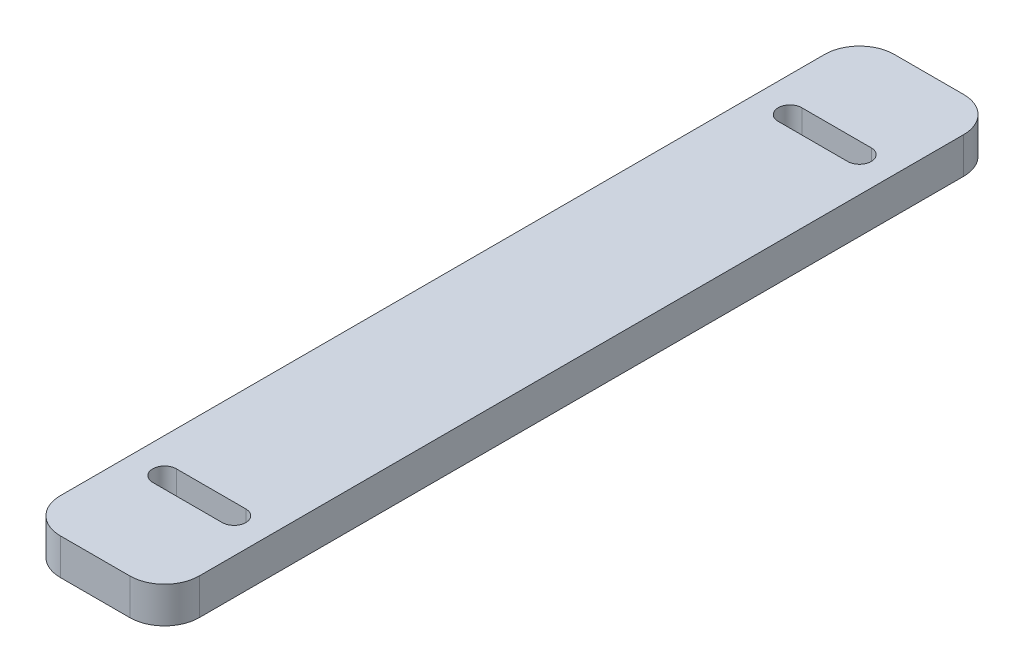
SolidWorks part; units mm, degrees
material "Acrylic (BLUE)"
ref_plane "Front Plane" through (0, 0, 0) normal (0, 0, 1) x (1, 0, 0)
ref_plane "Top Plane" through (0, 0, 0) normal (0, 1, 0) x (1, 0, 0)
ref_plane "Right Plane" through (0, 0, 0) normal (1, 0, 0) x (0, 0, -1)
sketch "Sketch1" plane through (0, 0, 0) normal (0, 1, 0) x (1, 0, 0)
  line L0 (-12.7, 76.2) -> (12.7, -76.2) construction
  line L1 (-12.7, 76.2) -> (12.7, 76.2)
  line L2 (-12.7, 76.2) -> (-12.7, -76.2)
  line L3 (-12.7, -76.2) -> (12.7, -76.2)
  line L4 (12.7, 76.2) -> (12.7, -76.2)
  dimension "D1" = 25.4
  dimension "D2" = 152.4
extrude "Boss-Extrude1" add sketch "Sketch1" along normal blind 6.604
sketch "Sketch2" plane through (0, 6.604, 0) normal (0, 1, 0) x (1, 0, 0)
  line L0 (0, 0) -> (0, 57.15) construction
  line L1 (-6.35, 57.15) -> (6.35, 57.15) construction
  line L2 (-6.35, 59.309) -> (6.35, 59.309)
  line L3 (-6.35, 54.991) -> (6.35, 54.991)
  line L4 (0, 0) -> (0, -57.15) construction
  line L5 (-6.35, -57.15) -> (6.35, -57.15) construction
  line L6 (-6.35, -54.991) -> (6.35, -54.991)
  line L7 (-6.35, -59.309) -> (6.35, -59.309)
  arc A0 (-6.35, 59.309) -> (-6.35, 54.991) centre (-6.35, 57.15) ccw
  arc A1 (6.35, 54.991) -> (6.35, 59.309) centre (6.35, 57.15) ccw
  arc A2 (-6.35, -54.991) -> (-6.35, -59.309) centre (-6.35, -57.15) ccw
  arc A3 (6.35, -59.309) -> (6.35, -54.991) centre (6.35, -57.15) ccw
  point P4 (0, 57.15)
  point P14 (0, -57.15)
  dimension "D1" = 57.15
  dimension "D2" = 4.318
  dimension "D3" = 12.7
extrude "Cut-Extrude1" cut sketch "Sketch2" against normal through all
fillet "Fillet1" radius 6.35 4 edges at (-12.7, 3.302, 76.2) (12.7, 3.302, 76.2) (-12.7, 3.302, -76.2) (12.7, 3.302, -76.2)
other "Move Face1" [suppressed] parameters "D1"=0.0508
